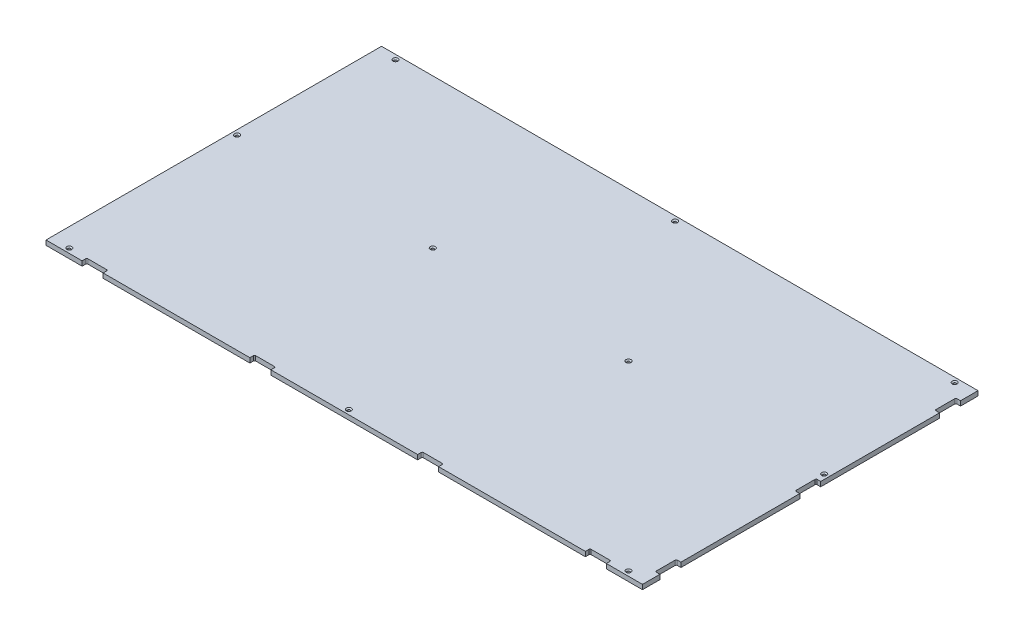
SolidWorks part; units mm, degrees
material "PE High Density"
ref_plane "Front Plane" through (0, 0, 0) normal (0, 0, 1) x (1, 0, 0)
ref_plane "Top Plane" through (0, 0, 0) normal (0, 1, 0) x (1, 0, 0)
ref_plane "Right Plane" through (0, 0, 0) normal (1, 0, 0) x (0, 0, -1)
sketch "Sketch1" plane through (0, 0, 0) normal (0, 1, 0) x (1, 0, 0)
  line L1 (0, 0) -> (1625.6, 0)
  line L2 (0, 0) -> (0, 914.4)
  line L3 (0, 914.4) -> (1625.6, 914.4)
  line L4 (1625.6, 0) -> (1625.6, 914.4)
  dimension "D1" = 1625.6
  dimension "D2" = 914.4
extrude "Boss-Extrude1" add sketch "Sketch1" along normal blind 12.7
sketch "Sketch2" plane through (0, 12.7, 0) normal (0, 1, 0) x (1, 0, 0)
  line L1 (1625.6, 914.4) -> (0, 914.4) construction
  line L2 (0, 914.4) -> (0, 0) construction
  line L3 (0, 0) -> (1625.6, 0) construction
  line L4 (1625.6, 0) -> (1625.6, 914.4) construction
  point P0 (12.7, 508)
  point P2 (546.1, 508)
  point P3 (1079.5, 508)
  point P4 (1612.9, 508)
  point P6 (50.8, 12.7)
  point P7 (812.8, 12.7)
  point P8 (1574.8, 12.7)
  point P9 (1574.8, 901.7)
  point P10 (812.8, 901.7)
  point P11 (50.8, 901.7)
  point P20 (812.8, 914.4)
  dimension "D1" = 12.7
  dimension "D2" = 12.7
  dimension "D3" = 12.7
  dimension "D4" = 12.7
  dimension "D5" = 266.7
  dimension "D6" = 533.4
  dimension "D7" = 762
  dimension "D8" = 762
  dimension "D10" = 406.4
hole_wizard "CSK for 1/4 Flat Head Machine Screw (100)1" positions "Sketch3" profile "Sketch4" countersink size "1/4" standard "ANSI Inch" end condition through all
sketch "Sketch3" plane through (0, 12.7, 0) normal (0, 1, 0) x (1, 0, 0)
  point P0 (12.7, 508)
  point P3 (50.8, 901.7)
  point P6 (546.1, 508)
  point P9 (812.8, 901.7)
  point P12 (1079.5, 508)
  point P15 (1574.8, 901.7)
  point P18 (1612.9, 508)
  point P24 (1574.8, 12.7)
  point P27 (812.8, 12.7)
  point P30 (50.8, 12.7)
sketch "Sketch4" plane through (12.7, 12.7, -508) normal (1, 0, 0) x (0, 0, 1)
  line L0 (0, 0) -> (0, 12.7)
  line L1 (0, 12.7) -> (3.5712, 12.7)
  line L2 (3.5712, 12.7) -> (3.5712, 2.7579)
  line L3 (3.5712, 2.7579) -> (6.858, 0)
  line L5 (6.858, 0) -> (0, 0)
  line L6 (-3.5712, 2.7579) -> (-6.858, 0) construction
  line L11 (0, -6.35) -> (0, 107.95) construction
  dimension "Thru Hole Dia." = 7.1425
  dimension "Thru Hole Depth" = 12.7
  dimension "Near C'Sink Dia." = 13.716
  dimension "Near C'Sink Angle" = 100
sketch "Sketch5" plane through (0, 12.7, 0) normal (0, 1, 0) x (1, 0, 0)
  line L1 (98.425, 0) -> (155.575, 0)
  line L2 (98.425, 0) -> (98.425, 12.7)
  line L3 (98.425, 12.7) -> (155.575, 12.7)
  line L4 (155.575, 0) -> (155.575, 12.7)
  line L6 (0, 0) -> (1625.6, 0) construction
  line L7 (0, 914.4) -> (0, 0) construction
  dimension "D1" = 98.425
  dimension "D2" = 57.15
  dimension "D3" = 12.7
extrude "Cut-Extrude1" cut sketch "Sketch5" against normal through all
pattern_linear "LPattern1" count 4 spacing 457.2 along (1, 0, 0) of "Cut-Extrude1"
sketch "Sketch6" plane through (0, 12.7, 0) normal (0, 1, 0) x (1, 0, 0)
  line L0 (1625.6, 0) -> (1625.6, 914.4) construction
  line L1 (1625.6, 47.625) -> (1612.9, 47.625)
  line L2 (1625.6, 47.625) -> (1625.6, 104.775)
  line L3 (1625.6, 104.775) -> (1612.9, 104.775)
  line L4 (1612.9, 47.625) -> (1612.9, 104.775)
  line L5 (1527.175, 0) -> (1625.6, 0) construction
  dimension "D1" = 12.7
  dimension "D2" = 57.15
  dimension "D3" = 47.625
extrude "Cut-Extrude2" cut sketch "Sketch6" against normal through all
pattern_linear "LPattern2" count 3 spacing 381 along (0, 0, -1) of "Cut-Extrude2"
fillet "Fillet1" radius 3.175 14 edges at (1012.825, 6.35, -12.7) (555.625, 6.35, -12.7) (98.425, 6.35, -12.7) (155.575, 6.35, -12.7) (612.775, 6.35, -12.7) (1069.975, 6.35, -12.7) (1470.025, 6.35, -12.7) (1527.175, 6.35, -12.7) (1612.9, 6.35, -47.625) (1612.9, 6.35, -104.775) (1612.9, 6.35, -485.775) (1612.9, 6.35, -428.625) (1612.9, 6.35, -809.625) (1612.9, 6.35, -866.775)
